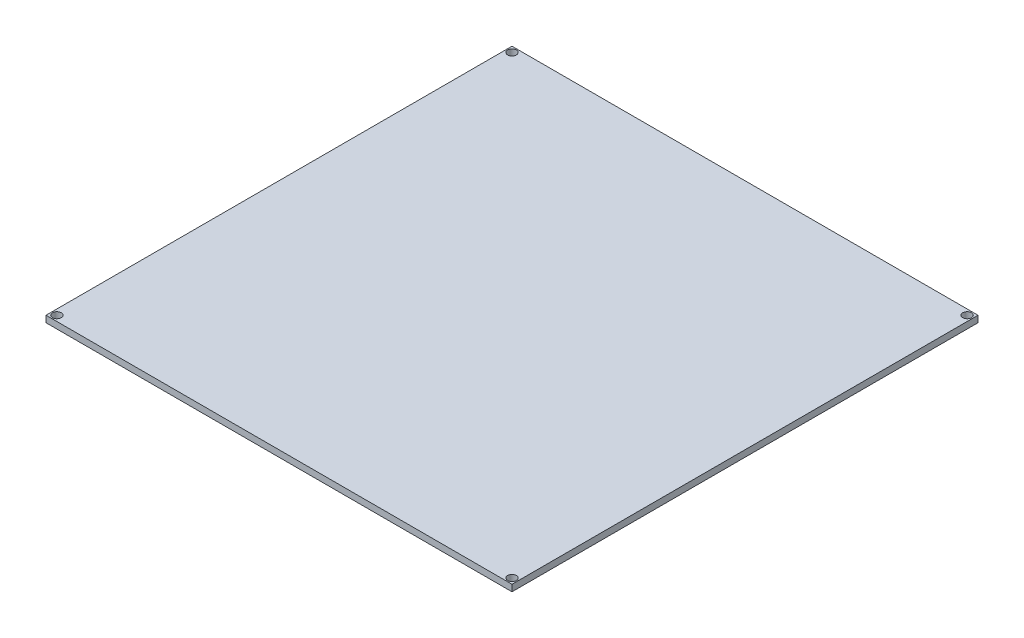
SolidWorks part; units mm, degrees
ref_plane "Front Plane" through (0, 0, 0) normal (0, 0, 1) x (1, 0, 0)
ref_plane "Top Plane" through (0, 0, 0) normal (0, 1, 0) x (1, 0, 0)
ref_plane "Right Plane" through (0, 0, 0) normal (1, 0, 0) x (0, 0, -1)
sketch "Sketch1" plane through (0, 0, 0) normal (0, 1, 0) x (1, 0, 0)
  line L1 (-107, -107) -> (107, -107)
  line L2 (-107, -107) -> (-107, 107)
  line L3 (-107, 107) -> (107, 107)
  line L4 (107, -107) -> (107, 107)
  line L5 (-107, -107) -> (107, 107) construction
  line L6 (-107, 107) -> (107, -107) construction
  circle A0 centre (-104.5, 104.5) radius 2
  circle A1 centre (104.5, 104.5) radius 2
  circle A2 centre (104.5, -104.5) radius 2
  circle A3 centre (-104.5, -104.5) radius 2
  point P0 (0, 0)
  point P8 (-104.4217, -60.4292)
  point P9 (0, 0)
  point P17 (0, 0)
  dimension "D3" = 209
  dimension "D4" = 4
  dimension "D1" = 214
  dimension "D2" = 4
extrude "Boss-Extrude1" add sketch "Sketch1" along normal blind 3
